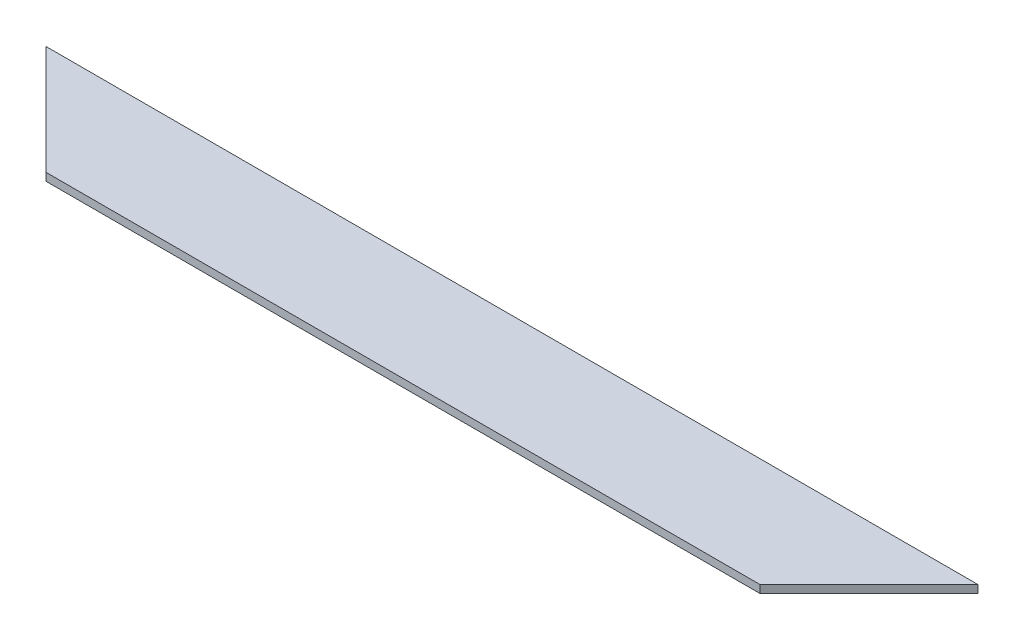
SolidWorks part; units mm, degrees
material "PC High Viscosity"
ref_plane "Front Plane" through (0, 0, 0) normal (0, 0, 1) x (1, 0, 0)
ref_plane "Top Plane" through (0, 0, 0) normal (0, 1, 0) x (1, 0, 0)
ref_plane "Right Plane" through (0, 0, 0) normal (1, 0, 0) x (0, 0, -1)
sketch "Sketch1" plane through (0, 0, 0) normal (0, 1, 0) x (1, 0, 0)
  line L0 (-469.9, 0) -> (469.9, 0)
  line L1 (469.9, 0) -> (381, -88.9)
  line L2 (381, -88.9) -> (-381, -88.9)
  line L3 (-381, -88.9) -> (-469.9, 0)
  line L4 (-381, -88.9) -> (-304.8, -165.1)
  line L5 (-304.8, -165.1) -> (304.8, -165.1)
  line L6 (304.8, -165.1) -> (381, -88.9)
  dimension "D1" = 45
  dimension "D2" = 939.8
  dimension "D3" = 88.9
  dimension "D5" = 165.1
  dimension "D6" = 609.6
extrude "Boss-Extrude1" add sketch "Sketch1" along normal blind 6.35 contours L3 L2 L1 L0
sketch "Sketch2" plane through (0, 6.35, 0) normal (0, 1, 0) x (1, 0, 0)
  line L0 (-380.0974, 0) -> (-291.1974, -88.9)
  line L1 (-469.9, 0) -> (469.9, 0) construction
  line L2 (381, -88.9) -> (-381, -88.9) construction
  line L3 (-291.1974, -88.9) -> (-381, -88.9)
  line L4 (-381, -88.9) -> (-469.9, 0)
  line L5 (-469.9, 0) -> (-380.0974, 0)
  dimension "D1" = 63.5
extrude "Cut-Extrude1" cut sketch "Sketch2" against normal blind 609.6
mirror "Mirror1" about plane through (0, 0, 0) normal (1, 0, 0) of "Cut-Extrude1"
